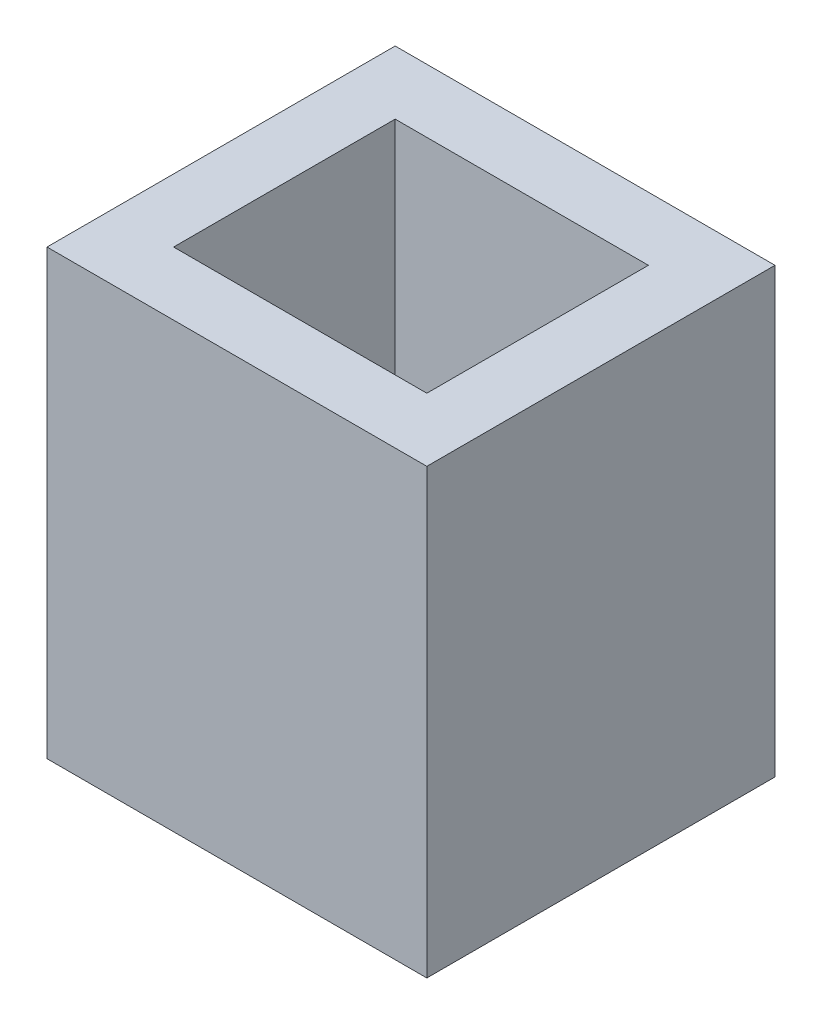
SolidWorks part; units mm, degrees
ref_plane "Front Plane" through (0, 0, 0) normal (0, 0, 1) x (1, 0, 0)
ref_plane "Top Plane" through (0, 0, 0) normal (0, 1, 0) x (1, 0, 0)
ref_plane "Right Plane" through (0, 0, 0) normal (1, 0, 0) x (0, 0, -1)
sketch "Sketch1" plane through (0, 0, 0) normal (0, 1, 0) x (1, 0, 0)
  line L1 (0, 0) -> (12, 0)
  line L2 (0, 0) -> (0, 11)
  line L3 (0, 11) -> (12, 11)
  line L4 (12, 0) -> (12, 11)
  dimension "D1" = 11
  dimension "D2" = 12
extrude "Boss-Extrude1" add sketch "Sketch1" along normal blind 14
shell "Shell1" thickness 2
sketch "Sketch2" plane through (0, 0, 0) normal (0, -1, 0) x (1, 0, 0)
  circle A0 centre (3.4529, -7.2899) radius 0.75
  circle A1 centre (5.9929, -7.2899) radius 0.75
  circle A2 centre (8.5329, -7.2899) radius 0.75
  point P0 (3.4529, -7.2899)
  point P1 (5.9929, -7.2899)
  point P2 (8.5329, -7.2899)
  dimension "D1" = 1.5
  dimension "D2" = 1.5
  dimension "D3" = 1.5
extrude "Cut-Extrude1" cut sketch "Sketch2" against normal blind 10
